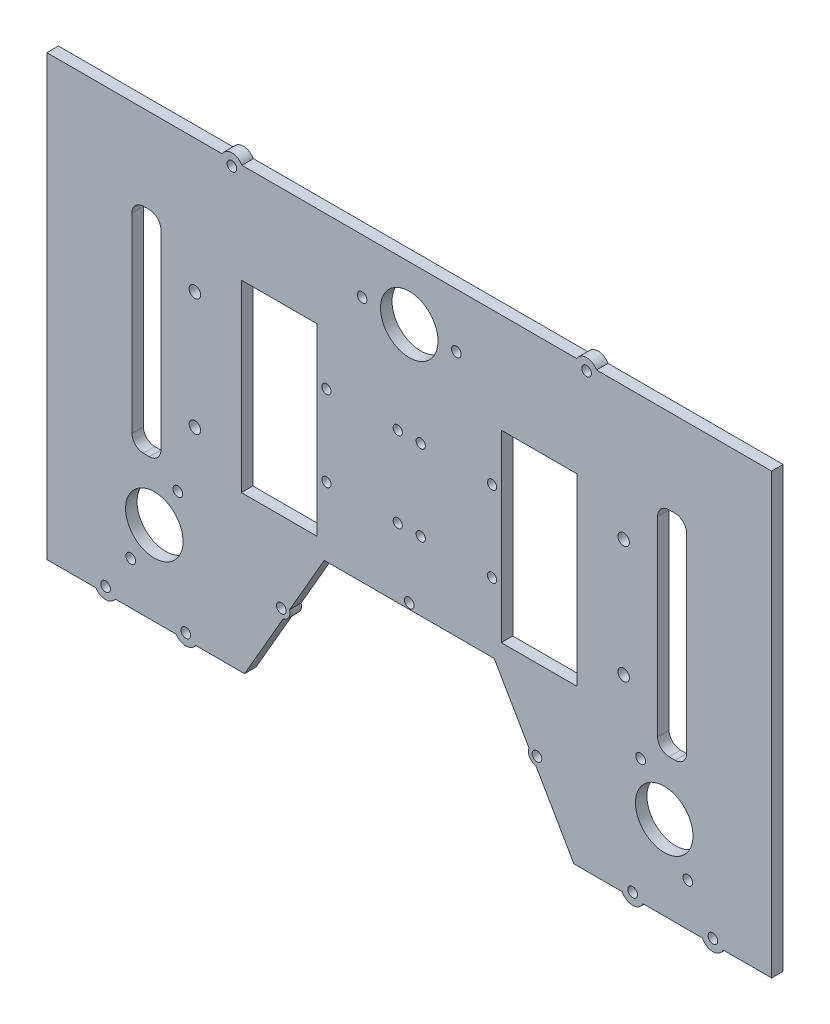
SolidWorks part; units mm, degrees
ref_plane "Front Plane" through (0, 0, 0) normal (0, 0, 1) x (1, 0, 0)
ref_plane "Top Plane" through (0, 0, 0) normal (0, 1, 0) x (1, 0, 0)
ref_plane "Right Plane" through (0, 0, 0) normal (1, 0, 0) x (0, 0, -1)
sketch "Sketch1" plane through (0, 0, 0) normal (0, 0, 1) x (1, 0, 0)
  line L0 (-73, -26.2703) -> (-40, -26.2703)
  line L1 (-73, 53.7297) -> (-73, -26.2703)
  line L2 (-40, 53.7297) -> (-73, 53.7297)
  line L3 (-40, -26.2703) -> (-40, 53.7297)
  line L4 (40, -26.2703) -> (73, -26.2703)
  line L5 (40, 53.7297) -> (40, -26.2703)
  line L6 (73, 53.7297) -> (40, 53.7297)
  line L7 (73, -26.2703) -> (73, 53.7297)
  line L8 (-112.97, 60.2225) -> (-115.57, 60.2225)
  line L9 (-107.97, -27.7632) -> (-107.97, 55.2225)
  line L10 (-115.57, -32.7632) -> (-112.97, -32.7632)
  line L11 (-120.57, 55.2225) -> (-120.57, -27.7632)
  line L12 (112.97, -32.7632) -> (115.57, -32.7632)
  line L13 (107.97, 55.2225) -> (107.97, -27.7632)
  line L14 (115.57, 60.2225) -> (112.97, 60.2225)
  line L15 (120.57, -27.7632) -> (120.57, 55.2225)
  line L16 (101.6451, -93.7703) -> (127.4976, -93.7703)
  line L17 (157.5513, -93.7703) -> (157.5513, 97.0831)
  line L18 (157.5513, 97.0831) -> (81.4311, 97.0831)
  line L19 (72.7709, 97.0831) -> (36.6509, 97.0831)
  line L20 (-36.6509, 97.0831) -> (-72.7708, 97.0831)
  line L21 (-81.431, 97.0831) -> (-157.5513, 97.0831)
  line L22 (-157.5513, 97.0831) -> (-157.5513, -93.7703)
  line L23 (-157.5513, -93.7703) -> (-136.2471, -93.7703)
  line L24 (-92.8957, -93.7703) -> (-71.5914, -93.7703)
  line L25 (-71.5914, -93.7703) -> (-54.8461, -64.7665)
  line L26 (-52.051, -59.9253) -> (-36.9504, -33.7703)
  line L27 (-36.9504, -33.7703) -> (36.9504, -33.7703)
  line L28 (36.9504, -33.7703) -> (52.0398, -59.906)
  line L29 (54.987, -65.0107) -> (71.5914, -93.7703)
  line L30 (71.5914, -93.7703) -> (92.6049, -93.7703)
  line L31 (-36.6509, 97.0831) -> (36.6509, 97.0831)
  line L32 (0, -33.7703) -> (0, -59.9253) construction
  line L33 (-71.5914, -93.7703) -> (-71.5914, -113.8608) construction
  line L34 (-71.5914, -113.8608) -> (-157.5513, -113.8608) construction
  line L35 (-157.5513, -113.8608) -> (-157.5513, -93.7703) construction
  line L36 (-114.5714, -113.8608) -> (-114.5714, -102.0308) construction
  line L37 (-127.7867, -93.7703) -> (-101.356, -93.7703)
  line L38 (71.5914, -93.7703) -> (71.5914, -109.5901) construction
  line L39 (71.5914, -109.5901) -> (157.5513, -109.5901) construction
  line L40 (157.5513, -109.5901) -> (157.5513, -93.7703) construction
  line L41 (114.5714, -109.5901) -> (114.5714, -120.746) construction
  line L42 (136.5378, -93.7703) -> (157.5513, -93.7703)
  circle A7 centre (20.5, 73.5179) radius 2.1
  circle A8 centre (-20.5, 73.5179) radius 2.1
  circle A9 centre (0, 73.5179) radius 12.5
  circle A13 centre (36, 31.2297) radius 2
  circle A14 centre (-5, -3.7703) radius 2
  circle A15 centre (5, -3.7703) radius 2
  circle A16 centre (36, -3.7703) radius 2
  circle A17 centre (-36, 31.2297) radius 2
  circle A18 centre (-5, 31.2297) radius 2
  circle A19 centre (5, 31.2297) radius 2
  circle A20 centre (-36, -3.7703) radius 2
  circle A21 centre (93.2, 39.2297) radius 2.5
  circle A22 centre (-93.2, 39.2297) radius 2.5
  circle A23 centre (-93.2, -11.7703) radius 2.5
  circle A24 centre (93.2, -11.7703) radius 2.5
  circle A26 centre (-77.1009, 94.5831) radius 2.1
  circle A29 centre (-97.1258, -91.1047) radius 2.1
  circle A30 centre (-55.6136, -61.0959) radius 2.1
  circle A31 centre (77.101, 94.5831) radius 2.1001
  circle A33 centre (97.125, -91.6329) radius 2.1
  circle A34 centre (55.5215, -61.299) radius 2.1
  circle A35 centre (-0.0002, -31.2703) radius 2.1002
  arc A36 (-115.57, 60.2225) -> (-120.57, 55.2225) centre (-115.57, 55.2225) ccw
  arc A37 (-107.97, 55.2225) -> (-112.97, 60.2225) centre (-112.97, 55.2225) ccw
  arc A38 (-112.97, -32.7632) -> (-107.97, -27.7632) centre (-112.97, -27.7632) ccw
  arc A39 (-120.57, -27.7632) -> (-115.57, -32.7632) centre (-115.57, -27.7632) ccw
  arc A40 (115.57, -32.7632) -> (120.57, -27.7632) centre (115.57, -27.7632) ccw
  arc A41 (107.97, -27.7632) -> (112.97, -32.7632) centre (112.97, -27.7632) ccw
  arc A42 (112.97, 60.2225) -> (107.97, 55.2225) centre (112.97, 55.2225) ccw
  arc A43 (120.57, 55.2225) -> (115.57, 60.2225) centre (115.57, 55.2225) ccw
  arc A44 (81.4311, 97.0831) -> (72.7709, 97.0831) centre (77.101, 94.5831) ccw
  arc A46 (-72.7708, 97.0831) -> (-81.431, 97.0831) centre (-77.1009, 94.5831) ccw
  arc A47 (-101.356, -93.7703) -> (-92.8957, -93.7703) centre (-97.1258, -91.1047) ccw
  arc A48 (-54.8461, -64.7665) -> (-52.051, -59.9253) centre (-55.6136, -61.0959) ccw
  arc A49 (52.0398, -59.906) -> (54.987, -65.0107) centre (55.5215, -61.299) ccw
  arc A50 (92.6049, -93.7703) -> (101.6451, -93.7703) centre (97.125, -91.6329) ccw
  circle A51 centre (-100.5921, -39.6299) radius 2.1
  circle A52 centre (-121.0921, -75.1369) radius 2.1
  circle A53 centre (-110.8421, -57.3834) radius 12.5
  circle A54 centre (-132.0169, -91.1047) radius 2.1
  arc A55 (-127.7867, -93.7703) -> (-136.2471, -93.7703) centre (-132.0169, -91.1047) cw
  circle A56 centre (132.0177, -91.6329) radius 2.1
  arc A57 (136.5378, -93.7703) -> (127.4976, -93.7703) centre (132.0177, -91.6329) cw
  circle A58 centre (121.0921, -75.1369) radius 2.1
  circle A59 centre (100.5921, -39.6299) radius 2.1
  circle A60 centre (110.8421, -57.3834) radius 12.5
  dimension "D1" = 19.7882
extrude "Boss-Extrude1" add sketch "Sketch1" along normal blind 5
